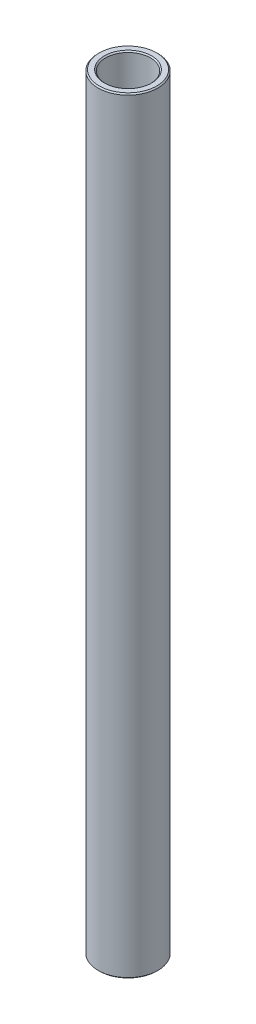
SolidWorks part; units mm, degrees
ref_plane "Front Plane" through (0, 0, 0) normal (0, 0, 1) x (1, 0, 0)
ref_plane "Top Plane" through (0, 0, 0) normal (0, 1, 0) x (1, 0, 0)
ref_plane "Right Plane" through (0, 0, 0) normal (1, 0, 0) x (0, 0, -1)
sketch "Sketch1" plane through (0, 0, 0) normal (0, 0, 1) x (1, 0, 0)
  line L0 (4.7625, 9.525) -> (4.7625, 172.3738)
  line L1 (4.7625, 172.3738) -> (6.35, 172.3738)
  line L2 (6.35, 172.3738) -> (6.35, 9.525)
  line L3 (6.35, 9.525) -> (4.7625, 9.525)
  line L6 (0, 0) -> (0, 181.8988) construction
  dimension "D1" = 9.525
  dimension "D2" = 9.525
  dimension "D3" = 12.7
  dimension "D4" = 9.525
revolve "Revolve1" add sketch "Sketch1" angle 360 about L6
chamfer "Chamfer1" distance 0.254 angle 45 4 edges at (6.35, 172.3738, 0) (4.7625, 172.3738, 0) (4.7625, 9.525, 0) (6.35, 9.525, 0)
equation "\"D4@Sketch1\"=\"D1@Sketch1\""
